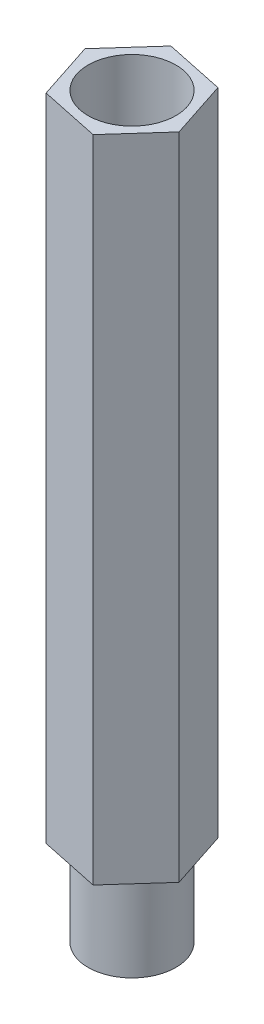
SolidWorks part; units mm, degrees
ref_plane "Front Plane" through (0, 0, 0) normal (0, 0, 1) x (1, 0, 0)
ref_plane "Top Plane" through (0, 0, 0) normal (0, 1, 0) x (1, 0, 0)
ref_plane "Right Plane" through (0, 0, 0) normal (1, 0, 0) x (0, 0, -1)
sketch "Sketch1" plane through (0, 0, 0) normal (0, 1, 0) x (1, 0, 0)
  line L1 (1.1562, 1.2896) -> (-0.5387, 1.6461)
  line L2 (-0.5387, 1.6461) -> (-1.695, 0.3565)
  line L3 (-1.695, 0.3565) -> (-1.1562, -1.2896)
  line L4 (-1.1562, -1.2896) -> (0.5387, -1.6461)
  line L5 (0.5387, -1.6461) -> (1.695, -0.3565)
  line L6 (1.695, -0.3565) -> (1.1562, 1.2896)
  circle A0 centre (0, 0) radius 1.5 construction
  dimension "D1" = 3
extrude "Boss-Extrude1" add sketch "Sketch1" along normal blind 18.5
sketch "Sketch2" plane through (0, 18.5, 0) normal (0, 1, 0) x (1, 0, 0)
  circle A0 centre (0, 0) radius 1.25
  dimension "D1" = 2.5
extrude "Cut-Extrude1" cut sketch "Sketch2" against normal up to surface (18.5 mm away) up to face at (0, 0, 0)
sketch "Sketch3" plane through (0, 0, 0) normal (0, -1, 0) x (1, 0, 0)
  circle A0 centre (0, 0) radius 1.25
extrude "Boss-Extrude2" add sketch "Sketch3" along normal blind 2.5 and the other way blind 2.5
